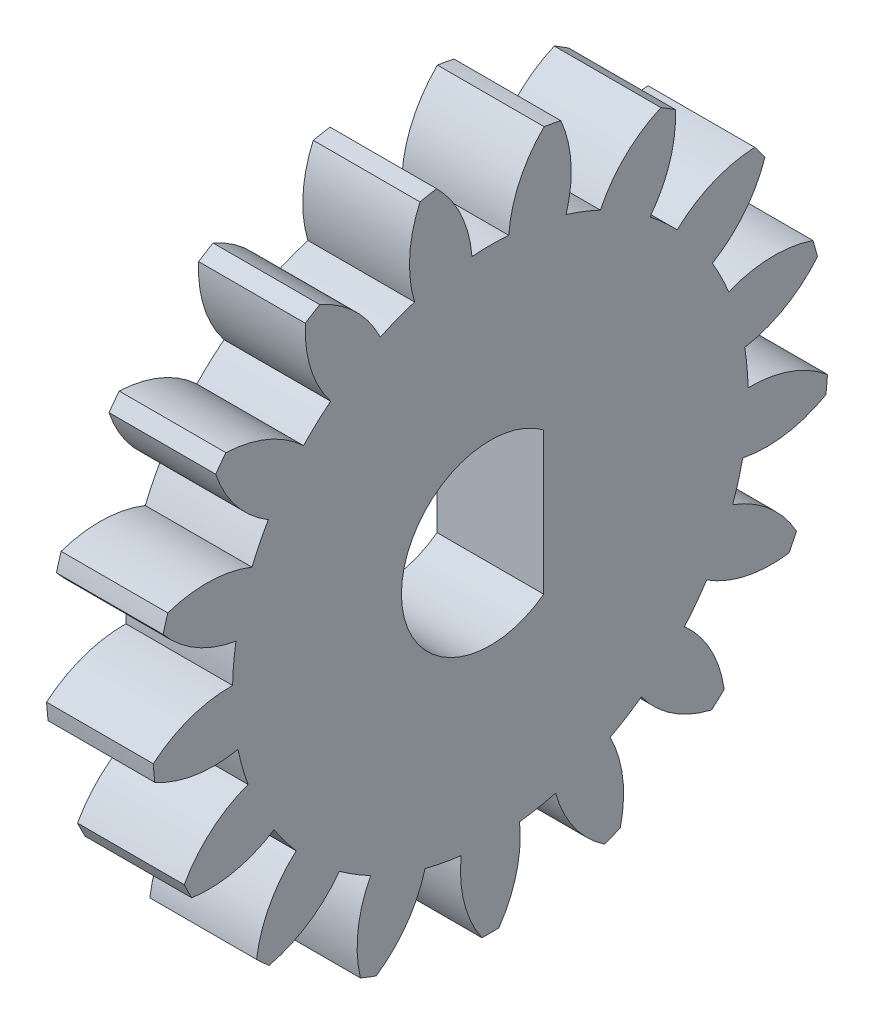
SolidWorks part; units mm, degrees
ref_plane "Plane1" through (0, 0, 0) normal (0, 0, 1) x (1, 0, 0)
ref_plane "Plane2" through (0, 0, 0) normal (0, 1, 0) x (1, 0, 0)
ref_plane "Plane3" through (0, 0, 0) normal (1, 0, 0) x (0, 0, -1)
other "Configuration Table"
sketch "HoldingSke" plane through (0, 0, 0) normal (0, 1, 0) x (1, 0, 0)
  line L0 (0, 0) -> (0.9563, -0.2924)
  line L1 (-15, 0) -> (100, 0) construction
  line L2 (0, 0) -> (-2.1039, 2.3779)
  line L3 (0, 0) -> (-11.863, 4.5341)
  line L4 (0, 0) -> (8.2586, 2.5249)
  line L5 (0, 0) -> (-46.8476, -17.4728)
  line L6 (0, 0) -> (-2.4869, -1.6779)
  line L7 (-2.1039, 2.3779) -> (8.6586, 51.2059)
  line L8 (-76.2, 54.61) -> (-75.3, 54.61)
  line L9 (-71.009, 38.7566) -> (-53.1078, 45.2721)
  line L10 (-76.2, 71.12) -> (104.1128, 71.12)
  line L11 (0, 0) -> (-3, 0)
  line L12 (-76.2, 101.6) -> (-76.162, 101.6)
  line L13 (24.9733, 27.94) -> (52.9518, 28.4284)
  line L14 (24.9733, 27.94) -> (24.9743, 27.94)
  line L15 (24.9733, 27.94) -> (100.4006, 29.5858)
  line L16 (-63.627, -1) -> (-12.827, -1)
  circle A0 centre (0, 0) radius 2.5
  circle A1 centre (0, 0) radius 7.249
  circle A2 centre (0, 0) radius 37.5
  circle A3 centre (0, 0) radius 2.5
  dimension "MHD" = 14.498
  dimension "Hub_dia" = 75
  dimension "Bore" = 5
  dimension "MBD" = 5
  dimension "Num_teeth" = 17
  dimension "Pitch" = 1
  dimension "Overall_len" = 50
  dimension "Show_teeth" = 17
  dimension "Thickness" = 3
  dimension "OAL" = 50.0001
  dimension "T_dim" = 0.9
  dimension "Ap" = 20
  dimension "H" = 19.05
  dimension "Pitch_radius" = 180.3128
  dimension "Width" = 3
  dimension "Backlash" = 0.038
  dimension "Addendum_fac" = 1
  dimension "Dedendum_fac" = 1.25
  dimension "Clearance_fac" = 0.25
  dimension "Dedendum_add" = 0.001
  dimension "Module" = 1
sketch "BasProSke" plane through (0, 0, 0) normal (0, 1, 0) x (1, 0, 0)
  line L0 (-10, 0) -> (60, 0) construction
  line L1 (0, 0) -> (0, 9.5)
  line L2 (0, 0) -> (3, 0)
  line L3 (3, 0) -> (3, 9.5)
  line L4 (3, 9.5) -> (0, 9.5)
  dimension "Thickness" = 3
  dimension "Diameter" = 19
revolve "Base-Revolve" add sketch "BasProSke" angle 360 about L0
sketch "TooCutSke" plane through (0, 0, 0) normal (1, 0, 0) x (0, 0, -1)
  line L1 (0, 0) -> (0, 107) construction
  line L2 (0, 0) -> (-0.8507, 8.4573) construction
  line L3 (0, 0) -> (-3.1126, 16.6509) construction
  line L4 (-0.8507, 8.4573) -> (-1.5563, 8.3254) construction
  arc A0 (0.5169, 7.2306) -> (-0.5169, 7.2306) centre (0, 0) ccw
  arc A1 (1.5331, 9.4012) -> (-1.5331, 9.4012) centre (0, 0) ccw
  circle A2 centre (0, 0) radius 8.5 construction
  circle A3 centre (0, 0) radius 7.9874 construction
  arc A4 (-0.5169, 7.2306) -> (-1.5331, 9.4012) centre (-3.9066, 6.9668) ccw
  arc A5 (1.5331, 9.4012) -> (0.5169, 7.2306) centre (3.9066, 6.9668) ccw
  dimension "Root_dia" = 14.498
  dimension "Overcut_dia" = 19.0508
  dimension "Pitch_dia" = 17
  dimension "Base_dia" = 15.9748
  dimension "Flank_rad" = 3.4
  dimension "Half_ang" = 10.588
  dimension "Half_CT" = 0.7178
extrude "ToothCut" cut sketch "TooCutSke" along normal through all
fillet "Breaks" [suppressed] radius 0.02
fillet "RootFillets" [suppressed] radius 0.251
pattern_circular "TeethCuts" count 17 every 21.176 about axis through (-10, 0, 0) along (1, 0, 0) of "ToothCut", "RootFillets", "Breaks"
sketch "HubNeaOneSke" plane through (0, 0, 0) normal (-1, 0, 0) x (0, 0, 1)
  circle A0 centre (0, 0) radius 7.249
  dimension "Diameter" = 14.498
extrude "HubNearOne" [suppressed] add sketch "HubNeaOneSke" along normal blind 47.0001
sketch "HubNeaBotSke" plane through (0, 0, 0) normal (-1, 0, 0) x (0, 0, 1)
  circle A0 centre (0, 0) radius 7.249
  dimension "Diameter" = 14.498
extrude "HubNearBoth" [suppressed] add sketch "HubNeaBotSke" along normal blind 23.5
ref_plane "FarPln" through (3, 0, 0) normal (1, 0, 0) x (0, 0, -1)
sketch "HubFarSke" plane through (3, 0, 0) normal (1, 0, 0) x (0, 0, -1)
  circle A0 centre (0, 0) radius 7.249
  dimension "Diameter" = 14.498
extrude "HubFar" [suppressed] add sketch "HubFarSke" along normal blind 23.5
sketch "BorSke" plane through (0, 0, 0) normal (1, 0, 0) x (0, 0, -1)
  circle A0 centre (0, 0) radius 2.5
  dimension "Diameter" = 5
extrude "Bore" cut sketch "BorSke" along normal mid plane 100.0001
sketch "KeySke" plane through (0, 0, 0) normal (1, 0, 0) x (0, 0, -1)
  line L0 (-1, 0) -> (-1, 3.4)
  line L1 (-1, 3.4) -> (1, 3.4)
  line L2 (1, 3.4) -> (1, 0)
  line L3 (0, 0) -> (0, 34) construction
  line L4 (-1, 0) -> (1, 0)
  dimension "Offset" = 3.4
  dimension "Width" = 2
extrude "Keyway" [suppressed] cut sketch "KeySke" along normal mid plane 100.0001
pattern_circular "Keyway2" [suppressed] count 2 every 90 about axis through (-10, 0, 0) along (1, 0, 0)
sketch "草图1" plane through (3, 0, 0) normal (1, 0, 0) x (0, 0, -1)
  line L0 (1.5, 2) -> (1.5, -2)
  arc A0 (1.5, -2) -> (1.5, 2) centre (0, 0) ccw
  dimension "D1" = 1.5
extrude "凸台-拉伸1" add sketch "草图1" against normal blind 3
equation "' \"Module@HoldingSke\" = 6.35"
equation "' \"Num_teeth@HoldingSke\" = 12"
equation "' \"Ap@HoldingSke\" =  20"
equation "' \"Ap@HoldingSke\" = 20"
equation "' \"Width@HoldingSke\" = 0.5 * 25.4"
equation "' \"Hub_dia@HoldingSke\"= 1 * 25.4"
equation "' \"Hub_dia@HoldingSke\" = 1 * 25.4"
equation "' \"Overall_len@HoldingSke\" = 1.0 * 25.4"
equation "' \"Bore@HoldingSke\" = 0.75 * 25.4"
equation "' \"T_dim@HoldingSke\" = 0.1 * 25.4"
equation "' \"Width@KeySke\" = 0.25 * 25.4"
equation "' \"Show_teeth@HoldingSke\" = 13"
equation "' \"Backlash@HoldingSke\" = 0.009 * 25.4"
equation "' \"Addendum_fac@HoldingSke\" = 1.0"
equation "' \"Dedendum_fac@HoldingSke\" = 1.25"
equation "' \"Dedendum_add@HoldingSke\" = 0.00005 * 25.4"
equation "' \"Clearance_fac@HoldingSke\" = 0.25"
equation "\"Pitch@HoldingSke\" = 1 / \"Module@HoldingSke\""
equation "\"Overcut_dia@TooCutSke\" = (\"Num_teeth@HoldingSke\" + 2 * \"Addendum_fac@HoldingSke\") / \"Pitch@HoldingSke\" + 0.002 * 25.4"
equation "\"Pitch_dia@TooCutSke\" = \"Num_teeth@HoldingSke\" / \"Pitch@HoldingSke\""
equation "\"Base_dia@TooCutSke\" = \"Num_teeth@HoldingSke\" / \"Pitch@HoldingSke\" * cos((\"Ap@HoldingSke\"  * 3.14159265 / 180))"
equation "\"Root_dia@TooCutSke\" = (\"Num_teeth@HoldingSke\" + 2) / \"Pitch@HoldingSke\" - 2 * (\"Addendum_fac@HoldingSke\" + \"Dedendum_fac@HoldingSke\") / \"Pitch@HoldingSke\" - \"Dedendum_add@HoldingSke\" * 2"
equation "\"Half_ang@TooCutSke\" = 180 / \"Num_teeth@HoldingSke\""
equation "\"Half_CT@TooCutSke\" = \"Num_teeth@HoldingSke\" / \"Pitch@HoldingSke\" * sin((3.14159265 / 2 / \"Num_teeth@HoldingSke\")) / 2 - 7 * \"Backlash@HoldingSke\" / 4"
equation "\"Flank_rad@TooCutSke\" = \"Num_teeth@HoldingSke\" / \"Pitch@HoldingSke\" / 5"
equation "\"Radius@RootFillets\" = \"Clearance_fac@HoldingSke\" / \"Pitch@HoldingSke\" + \"Dedendum_add@HoldingSke\""
equation "\"Break_rad@Breaks\" = 0.02 / \"Pitch@HoldingSke\""
equation "\"Thickness@HoldingSke\" = \"Width@HoldingSke\""
equation "\"OAL@HoldingSke\" = \"Thickness@HoldingSke\""
equation "\"MHD@HoldingSke\" = (\"Num_teeth@HoldingSke\" + 2) / \"Pitch@HoldingSke\" - 2 * (\"Addendum_fac@HoldingSke\" + \"Dedendum_fac@HoldingSke\")  / \"Pitch@HoldingSke\" - \"Dedendum_add@HoldingSke\" * 2"
equation "\"MBD@HoldingSke\" = (\"Num_teeth@HoldingSke\" + 2) / \"Pitch@HoldingSke\" - 2 * (\"Addendum_fac@HoldingSke\" + \"Dedendum_fac@HoldingSke\")  / \"Pitch@HoldingSke\" - \"Dedendum_add@HoldingSke\" * 2 - 0.002 * 25.4"
equation "\"MHD@HoldingSke\" = ((sgn( \"MHD@HoldingSke\" - \"Hub_dia@HoldingSke\" )-1)*( \"MHD@HoldingSke\" - \"Hub_dia@HoldingSke\" ))/-2+ \"Hub_dia@HoldingSke\""
equation "\"MBD@HoldingSke\" = ((sgn( \"MBD@HoldingSke\" - \"Bore@HoldingSke\" )-1)*( \"MBD@HoldingSke\" - \"Bore@HoldingSke\" ))/-2+ \"Bore@HoldingSke\""
equation "\"OAL@HoldingSke\" = ((sgn( \"OAL@HoldingSke\" - \"Overall_len@HoldingSke\" )+1)*( \"OAL@HoldingSke\" - \"Overall_len@HoldingSke\" ))/2 + \"Overall_len@HoldingSke\" + 0.000002 * 25.4"
equation "\"Num_teeth@TeethCuts\" = int( \"Show_teeth@HoldingSke\" ) + 1"
equation "\"Num_teeth@TeethCuts\" = ((sgn( \"Num_teeth@TeethCuts\" - \"Num_teeth@HoldingSke\" )-1)*( \"Num_teeth@TeethCuts\" - \"Num_teeth@HoldingSke\" ))/-2+ \"Num_teeth@HoldingSke\""
equation "\"Num_teeth@TeethCuts\" = ((sgn( \"Num_teeth@TeethCuts\" - 2.0)+1)*( \"Num_teeth@TeethCuts\" - 2.0))/2 +2.0"
equation "\"Angle@TeethCuts\" = 360.0 / \"Num_teeth@HoldingSke\""
equation "\"Diameter@BasProSke\" = (\"Num_teeth@HoldingSke\" + 2 * \"Addendum_fac@HoldingSke\") / \"Pitch@HoldingSke\""
equation "\"Thickness@BasProSke\"  = \"Thickness@HoldingSke\""
equation "' \"Fillet_rad@BasProSke\" =  \"Thickness@HoldingSke\" * 0.05"
equation "' \"Fillet_rad@BasProSke\" = \"Thickness@HoldingSke\" * 0.05"
equation "\"MHD@HoldingSke\" = ((sgn( \"MHD@HoldingSke\" - \"Root_dia@TooCutSke\" )-1)*( \"MHD@HoldingSke\" - \"Root_dia@TooCutSke\" ))/-2+ \"Root_dia@TooCutSke\""
equation "\"Diameter@HubNeaOneSke\" = \"MHD@HoldingSke\""
equation "\"Length@HubNearOne\" = \"OAL@HoldingSke\" - \"Thickness@BasProSke\""
equation "\"Diameter@HubNeaBotSke\" = \"MHD@HoldingSke\""
equation "\"Length@HubNearBoth\" = ( \"OAL@HoldingSke\" - \"Thickness@BasProSke\" ) / 2.0"
equation "\"Thickness@FarPln\" = \"Thickness@BasProSke\""
equation "\"Diameter@HubFarSke\" = \"MHD@HoldingSke\""
equation "\"Length@HubFar\" = ( \"OAL@HoldingSke\" - \"Thickness@BasProSke\" ) / 2.0"
equation "\"Diameter@BorSke\" = \"MBD@HoldingSke\""
equation "\"D1@Bore\" = \"OAL@HoldingSke\" * 2.0"
equation "\"D1@Keyway\" = \"OAL@HoldingSke\" * 2.0"
equation "\"Offset@KeySke\" = \"T_dim@HoldingSke\" + \"MBD@HoldingSke\" / 2.0"
